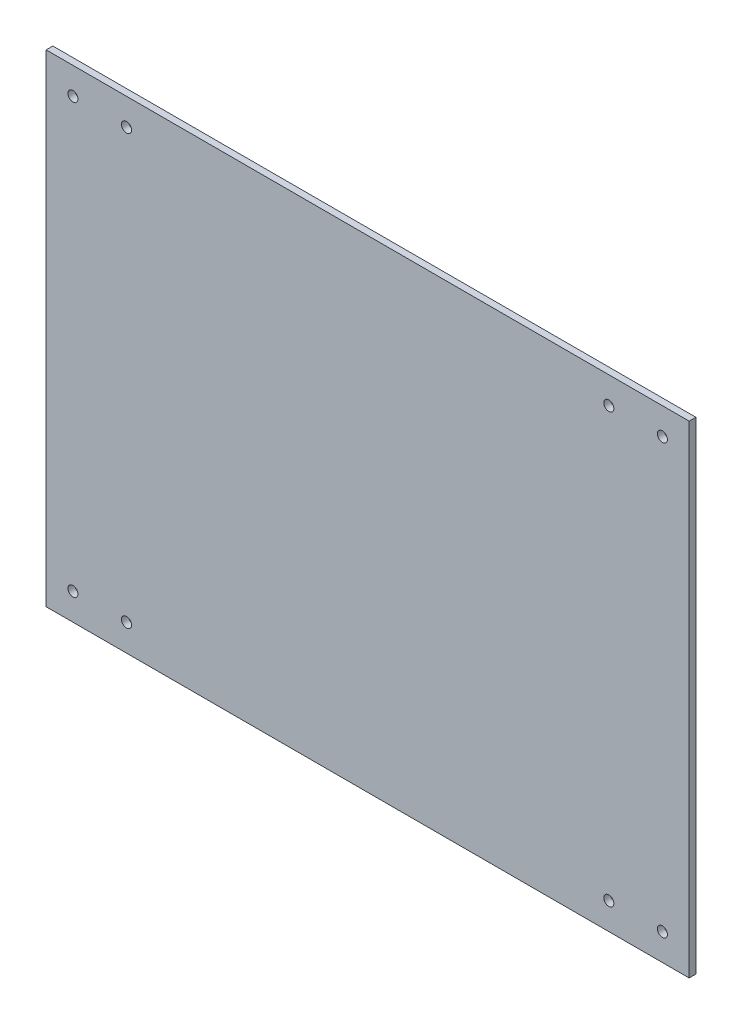
SolidWorks part; units mm, degrees
ref_plane "Front Plane" through (0, 0, 0) normal (0, 0, 1) x (1, 0, 0)
ref_plane "Top Plane" through (0, 0, 0) normal (0, 1, 0) x (1, 0, 0)
ref_plane "Right Plane" through (0, 0, 0) normal (1, 0, 0) x (0, 0, -1)
sketch "Sketch1" plane through (0, 0, 0) normal (0, 0, 1) x (1, 0, 0)
  line L0 (-139.7, 114.3) -> (-139.7, -114.3) construction
  line L1 (152.4, -114.3) -> (-152.4, -114.3)
  line L2 (152.4, -114.3) -> (152.4, 114.3)
  line L3 (152.4, 114.3) -> (-152.4, 114.3)
  line L4 (-152.4, -114.3) -> (-152.4, 114.3)
  line L5 (152.4, -114.3) -> (-152.4, 114.3) construction
  line L6 (152.4, 114.3) -> (-152.4, -114.3) construction
  line L7 (-152.4, 101.6) -> (152.4, 101.6) construction
  line L8 (139.7, 114.3) -> (139.7, -114.3) construction
  line L9 (-152.4, -101.6) -> (152.4, -101.6) construction
  line L10 (-114.3, 101.6) -> (-114.3, -101.6) construction
  line L11 (114.3, 101.6) -> (114.3, -101.6) construction
  circle A0 centre (139.7, 101.6) radius 2.3813
  circle A1 centre (-139.7, 101.6) radius 2.3813
  circle A2 centre (-139.7, -101.6) radius 2.3813
  circle A3 centre (139.7, -101.6) radius 2.3813
  circle A4 centre (114.3, 101.6) radius 2.3813
  circle A6 centre (-114.3, 101.6) radius 2.3813
  circle A7 centre (-114.3, -101.6) radius 2.3813
  circle A8 centre (114.3, -101.6) radius 2.3813
  point P0 (0, 0)
  point P14 (-139.7, 101.6)
  point P16 (-139.7, -101.6)
  point P17 (139.7, -101.6)
  point P18 (139.7, 101.6)
  dimension "D7" = 4.7625
  dimension "D1" = 304.8
  dimension "D2" = 228.6
  dimension "D3" = 12.7
  dimension "D4" = 12.7
  dimension "D5" = 12.7
  dimension "D6" = 12.7
  dimension "D8" = 25.4
  dimension "D9" = 25.4
extrude "Boss-Extrude1" add sketch "Sketch1" along normal blind 3.175
